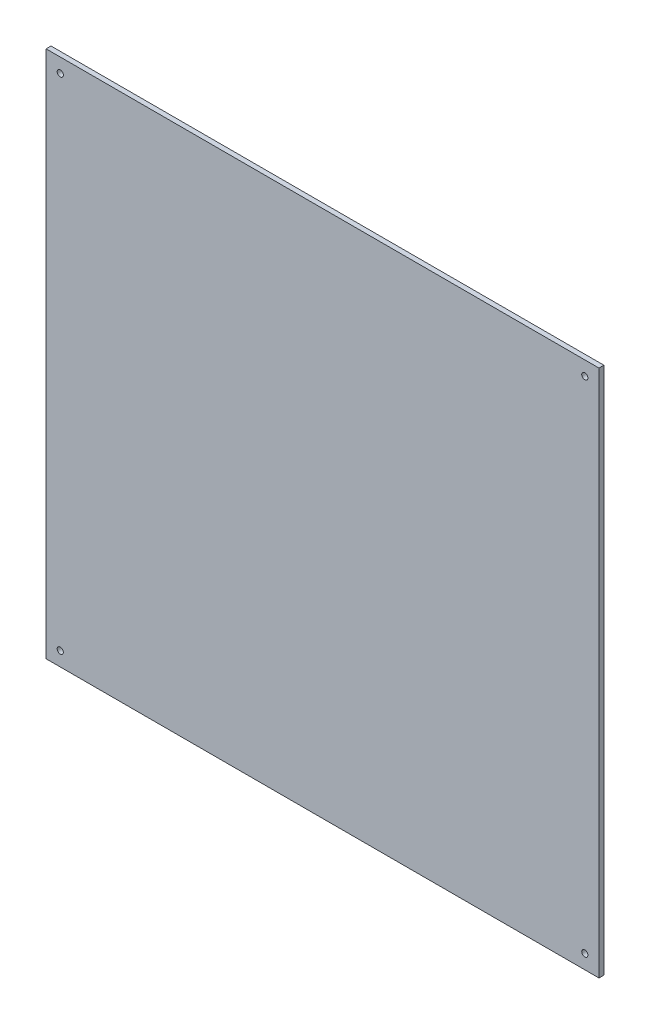
SolidWorks part; units mm, degrees
material "Acrilico (impatto medio-alto)"
ref_plane "Piano frontale" through (0, 0, 0) normal (0, 0, 1) x (1, 0, 0)
ref_plane "Piano superiore" through (0, 0, 0) normal (0, 1, 0) x (1, 0, 0)
ref_plane "Piano destro" through (0, 0, 0) normal (1, 0, 0) x (0, 0, -1)
sketch "Schizzo1" plane through (0, 0, 0) normal (0, 0, 1) x (1, 0, 0)
  line L0 (-224.5, 429) -> (-224.5, 0) construction
  line L1 (0, 0) -> (-449, 0)
  line L2 (0, 0) -> (0, 429)
  line L3 (0, 429) -> (-449, 429)
  line L4 (-449, 0) -> (-449, 429)
  line L5 (-449, 214.5) -> (0, 214.5) construction
  circle A0 centre (-437.5, 417.5) radius 2.5
  circle A1 centre (-11.5, 417.5) radius 2.5
  circle A2 centre (-437.5, 11.5) radius 2.5
  circle A3 centre (-11.5, 11.5) radius 2.5
  point P9 (-224.5, 214.5)
  dimension "D3" = 11.5
  dimension "D2" = 5
  dimension "D1" = 449
  dimension "314" = 429
  dimension "D4" = 11.5
extrude "Estrusione-Estrusione1" add sketch "Schizzo1" along normal blind 4
